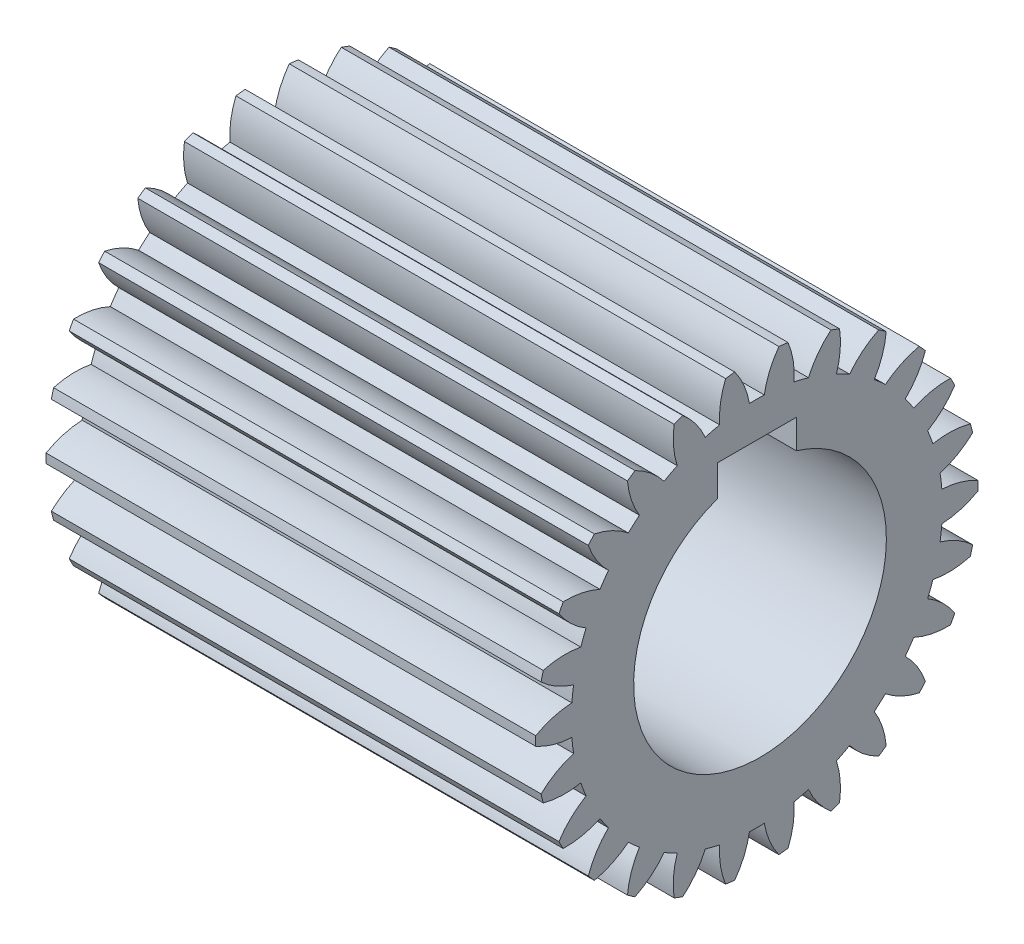
SolidWorks part; units mm, degrees
ref_plane "Plane1" through (0, 0, 0) normal (0, 0, 1) x (1, 0, 0)
ref_plane "Plane2" through (0, 0, 0) normal (0, 1, 0) x (1, 0, 0)
ref_plane "Plane3" through (0, 0, 0) normal (1, 0, 0) x (0, 0, -1)
sketch "HoldingSke" plane through (0, 0, 0) normal (0, 1, 0) x (1, 0, 0)
  line L0 (0, 0) -> (0.4494, -0.2192)
  line L1 (-15, 0) -> (100, 0) construction
  line L2 (0, 0) -> (-2.1039, 2.3779)
  line L3 (0, 0) -> (-11.863, 4.5341)
  line L4 (0, 0) -> (7.762, 3.7858)
  line L5 (0, 0) -> (-46.8476, -17.4728)
  line L6 (0, 0) -> (-51.3957, -34.6768)
  line L7 (-2.1039, 2.3779) -> (11.2416, 62.9246)
  line L8 (-76.2, 54.61) -> (-76.1, 54.61)
  line L9 (-71.009, 38.7566) -> (-53.1078, 45.2721)
  line L10 (-76.2, 71.12) -> (104.1128, 71.12)
  line L11 (0, 0) -> (-62, 0)
  line L12 (-76.2, 101.6) -> (-76.133, 101.6)
  line L13 (24.9733, 27.94) -> (52.9518, 28.4284)
  line L14 (24.9733, 27.94) -> (24.9743, 27.94)
  line L15 (24.9733, 27.94) -> (100.4006, 29.5858)
  line L16 (-63.627, -2) -> (-12.827, -2)
  circle A0 centre (0, 0) radius 0.4
  circle A1 centre (0, 0) radius 23.499
  circle A2 centre (0, 0) radius 37.5
  circle A3 centre (0, 0) radius 0.4
  dimension "MHD" = 46.998
  dimension "Hub_dia" = 75
  dimension "Bore" = 0.8
  dimension "MBD" = 0.8
  dimension "Num_teeth" = 26
  dimension "Pitch" = 0.5
  dimension "Overall_len" = 50
  dimension "Show_teeth" = 26
  dimension "Thickness" = 62
  dimension "OAL" = 62.0001
  dimension "T_dim" = 0.1
  dimension "Ap" = 20
  dimension "H" = 19.05
  dimension "Pitch_radius" = 180.3128
  dimension "Width" = 62
  dimension "Backlash" = 0.067
  dimension "Addendum_fac" = 1
  dimension "Dedendum_fac" = 1.25
  dimension "Clearance_fac" = 0.25
  dimension "Dedendum_add" = 0.001
  dimension "Module" = 2
sketch "BasProSke" plane through (0, 0, 0) normal (0, 1, 0) x (1, 0, 0)
  line L0 (-10, 0) -> (60, 0) construction
  line L1 (0, 0) -> (0, 28)
  line L2 (0, 0) -> (62, 0)
  line L3 (62, 0) -> (62, 28)
  line L4 (62, 28) -> (0, 28)
  dimension "Thickness" = 62
  dimension "Diameter" = 56
revolve "Base-Revolve" add sketch "BasProSke" angle 360 about L0
sketch "TooCutSke" plane through (0, 0, 0) normal (1, 0, 0) x (0, 0, -1)
  line L1 (0, 0) -> (0, 107) construction
  line L2 (0, 0) -> (-1.6871, 25.9452) construction
  line L3 (0, 0) -> (-6.2581, 51.5402) construction
  line L4 (-1.6871, 25.9452) -> (-3.1291, 25.7701) construction
  arc A0 (0.9399, 23.4802) -> (-0.9399, 23.4802) centre (0, 0) ccw
  arc A1 (2.8138, 27.8838) -> (-2.8138, 27.8838) centre (0, 0) ccw
  circle A2 centre (0, 0) radius 26 construction
  circle A3 centre (0, 0) radius 24.432 construction
  arc A4 (-0.9399, 23.4802) -> (-2.8138, 27.8838) centre (-11.1896, 21.719) ccw
  arc A5 (2.8138, 27.8838) -> (0.9399, 23.4802) centre (11.1896, 21.719) ccw
  dimension "Root_dia" = 46.998
  dimension "Overcut_dia" = 56.0508
  dimension "Pitch_dia" = 52
  dimension "Base_dia" = 48.864
  dimension "Flank_rad" = 10.4
  dimension "Half_ang" = 6.923
  dimension "Half_CT" = 1.4526
extrude "ToothCut" cut sketch "TooCutSke" along normal through all
fillet "Breaks" [suppressed] radius 0.04
fillet "RootFillets" [suppressed] radius 0.501
pattern_circular "TeethCuts" count 26 every 13.846 about axis through (-10, 0, 0) along (1, 0, 0) of "ToothCut", "RootFillets", "Breaks"
sketch "HubNeaOneSke" plane through (0, 0, 0) normal (-1, 0, 0) x (0, 0, 1)
  circle A0 centre (0, 0) radius 23.499
  dimension "Diameter" = 46.998
extrude "HubNearOne" [suppressed] add sketch "HubNeaOneSke" along normal blind 12.7001
sketch "HubNeaBotSke" plane through (0, 0, 0) normal (-1, 0, 0) x (0, 0, 1)
  circle A0 centre (0, 0) radius 23.499
  dimension "Diameter" = 46.998
extrude "HubNearBoth" [suppressed] add sketch "HubNeaBotSke" along normal blind 6.35
ref_plane "FarPln" through (62, 0, 0) normal (1, 0, 0) x (0, 0, -1)
sketch "HubFarSke" plane through (62, 0, 0) normal (1, 0, 0) x (0, 0, -1)
  circle A0 centre (0, 0) radius 23.499
  dimension "Diameter" = 46.998
extrude "HubFar" [suppressed] add sketch "HubFarSke" along normal blind 6.35
sketch "BorSke" plane through (0, 0, 0) normal (1, 0, 0) x (0, 0, -1)
  circle A0 centre (0, 0) radius 0.4
  dimension "Diameter" = 0.8
extrude "Bore" cut sketch "BorSke" along normal mid plane 124.0001
sketch "KeySke" plane through (0, 0, 0) normal (1, 0, 0) x (0, 0, -1)
  line L0 (-0.05, 0) -> (-0.05, 0.5)
  line L1 (-0.05, 0.5) -> (0.05, 0.5)
  line L2 (0.05, 0.5) -> (0.05, 0)
  line L3 (0, 0) -> (0, 34) construction
  line L4 (-0.05, 0) -> (0.05, 0)
  dimension "Offset" = 0.5
  dimension "Width" = 0.1
extrude "Keyway" [suppressed] cut sketch "KeySke" along normal mid plane 124.0001
pattern_circular "Keyway2" [suppressed] count 2 every 90 about axis through (-10, 0, 0) along (1, 0, 0)
sketch "Sketch1" plane through (62, 0, 0) normal (1, 0, 0) x (0, 0, -1)
  line L0 (0, 0) -> (0, 22.4761) construction
  line L2 (-5, 19) -> (5, 19)
  line L3 (-5, 19) -> (-5, 15.0612)
  line L5 (5, 19) -> (5, 15.3245)
  arc A0 (-5, 15.0612) -> (5, 15.3245) centre (0.4, 0) ccw
  circle A1 centre (0, 0) radius 0.4 construction
  dimension "D1" = 32
  dimension "D2" = 10
  dimension "D3" = 19
extrude "Cut-Extrude1" cut sketch "Sketch1" against normal through all contours A0 L5 L2 L3
equation "' \"Module@HoldingSke\" = 6.35"
equation "' \"Num_teeth@HoldingSke\" = 12"
equation "' \"Ap@HoldingSke\" =  20"
equation "' \"Ap@HoldingSke\" = 20"
equation "' \"Width@HoldingSke\" = 0.5 * 25.4"
equation "' \"Hub_dia@HoldingSke\"= 1 * 25.4"
equation "' \"Hub_dia@HoldingSke\" = 1 * 25.4"
equation "' \"Overall_len@HoldingSke\" = 1.0 * 25.4"
equation "' \"Bore@HoldingSke\" = 0.75 * 25.4"
equation "' \"T_dim@HoldingSke\" = 0.1 * 25.4"
equation "' \"Width@KeySke\" = 0.25 * 25.4"
equation "' \"Show_teeth@HoldingSke\" = 13"
equation "' \"Backlash@HoldingSke\" = 0.009 * 25.4"
equation "' \"Addendum_fac@HoldingSke\" = 1.0"
equation "' \"Dedendum_fac@HoldingSke\" = 1.25"
equation "' \"Dedendum_add@HoldingSke\" = 0.00005 * 25.4"
equation "' \"Clearance_fac@HoldingSke\" = 0.25"
equation "\"Pitch@HoldingSke\" = 1 / \"Module@HoldingSke\""
equation "\"Overcut_dia@TooCutSke\" = (\"Num_teeth@HoldingSke\" + 2 * \"Addendum_fac@HoldingSke\") / \"Pitch@HoldingSke\" + 0.002 * 25.4"
equation "\"Pitch_dia@TooCutSke\" = \"Num_teeth@HoldingSke\" / \"Pitch@HoldingSke\""
equation "\"Base_dia@TooCutSke\" = \"Num_teeth@HoldingSke\" / \"Pitch@HoldingSke\" * cos((\"Ap@HoldingSke\"  * 3.14159265 / 180))"
equation "\"Root_dia@TooCutSke\" = (\"Num_teeth@HoldingSke\" + 2) / \"Pitch@HoldingSke\" - 2 * (\"Addendum_fac@HoldingSke\" + \"Dedendum_fac@HoldingSke\") / \"Pitch@HoldingSke\" - \"Dedendum_add@HoldingSke\" * 2"
equation "\"Half_ang@TooCutSke\" = 180 / \"Num_teeth@HoldingSke\""
equation "\"Half_CT@TooCutSke\" = \"Num_teeth@HoldingSke\" / \"Pitch@HoldingSke\" * sin((3.14159265 / 2 / \"Num_teeth@HoldingSke\")) / 2 - 7 * \"Backlash@HoldingSke\" / 4"
equation "\"Flank_rad@TooCutSke\" = \"Num_teeth@HoldingSke\" / \"Pitch@HoldingSke\" / 5"
equation "\"Radius@RootFillets\" = \"Clearance_fac@HoldingSke\" / \"Pitch@HoldingSke\" + \"Dedendum_add@HoldingSke\""
equation "\"Break_rad@Breaks\" = 0.02 / \"Pitch@HoldingSke\""
equation "\"Thickness@HoldingSke\" = \"Width@HoldingSke\""
equation "\"OAL@HoldingSke\" = \"Thickness@HoldingSke\""
equation "\"MHD@HoldingSke\" = (\"Num_teeth@HoldingSke\" + 2) / \"Pitch@HoldingSke\" - 2 * (\"Addendum_fac@HoldingSke\" + \"Dedendum_fac@HoldingSke\")  / \"Pitch@HoldingSke\" - \"Dedendum_add@HoldingSke\" * 2"
equation "\"MBD@HoldingSke\" = (\"Num_teeth@HoldingSke\" + 2) / \"Pitch@HoldingSke\" - 2 * (\"Addendum_fac@HoldingSke\" + \"Dedendum_fac@HoldingSke\")  / \"Pitch@HoldingSke\" - \"Dedendum_add@HoldingSke\" * 2 - 0.002 * 25.4"
equation "\"MHD@HoldingSke\" = ((sgn( \"MHD@HoldingSke\" - \"Hub_dia@HoldingSke\" )-1)*( \"MHD@HoldingSke\" - \"Hub_dia@HoldingSke\" ))/-2+ \"Hub_dia@HoldingSke\""
equation "\"MBD@HoldingSke\" = ((sgn( \"MBD@HoldingSke\" - \"Bore@HoldingSke\" )-1)*( \"MBD@HoldingSke\" - \"Bore@HoldingSke\" ))/-2+ \"Bore@HoldingSke\""
equation "\"OAL@HoldingSke\" = ((sgn( \"OAL@HoldingSke\" - \"Overall_len@HoldingSke\" )+1)*( \"OAL@HoldingSke\" - \"Overall_len@HoldingSke\" ))/2 + \"Overall_len@HoldingSke\" + 0.000002 * 25.4"
equation "\"Num_teeth@TeethCuts\" = int( \"Show_teeth@HoldingSke\" ) + 1"
equation "\"Num_teeth@TeethCuts\" = ((sgn( \"Num_teeth@TeethCuts\" - \"Num_teeth@HoldingSke\" )-1)*( \"Num_teeth@TeethCuts\" - \"Num_teeth@HoldingSke\" ))/-2+ \"Num_teeth@HoldingSke\""
equation "\"Num_teeth@TeethCuts\" = ((sgn( \"Num_teeth@TeethCuts\" - 2.0)+1)*( \"Num_teeth@TeethCuts\" - 2.0))/2 +2.0"
equation "\"Angle@TeethCuts\" = 360.0 / \"Num_teeth@HoldingSke\""
equation "\"Diameter@BasProSke\" = (\"Num_teeth@HoldingSke\" + 2 * \"Addendum_fac@HoldingSke\") / \"Pitch@HoldingSke\""
equation "\"Thickness@BasProSke\"  = \"Thickness@HoldingSke\""
equation "' \"Fillet_rad@BasProSke\" =  \"Thickness@HoldingSke\" * 0.05"
equation "' \"Fillet_rad@BasProSke\" = \"Thickness@HoldingSke\" * 0.05"
equation "\"MHD@HoldingSke\" = ((sgn( \"MHD@HoldingSke\" - \"Root_dia@TooCutSke\" )-1)*( \"MHD@HoldingSke\" - \"Root_dia@TooCutSke\" ))/-2+ \"Root_dia@TooCutSke\""
equation "\"Diameter@HubNeaOneSke\" = \"MHD@HoldingSke\""
equation "\"Length@HubNearOne\" = \"OAL@HoldingSke\" - \"Thickness@BasProSke\""
equation "\"Diameter@HubNeaBotSke\" = \"MHD@HoldingSke\""
equation "\"Length@HubNearBoth\" = ( \"OAL@HoldingSke\" - \"Thickness@BasProSke\" ) / 2.0"
equation "\"Thickness@FarPln\" = \"Thickness@BasProSke\""
equation "\"Diameter@HubFarSke\" = \"MHD@HoldingSke\""
equation "\"Length@HubFar\" = ( \"OAL@HoldingSke\" - \"Thickness@BasProSke\" ) / 2.0"
equation "\"Diameter@BorSke\" = \"MBD@HoldingSke\""
equation "\"D1@Bore\" = \"OAL@HoldingSke\" * 2.0"
equation "\"D1@Keyway\" = \"OAL@HoldingSke\" * 2.0"
equation "\"Offset@KeySke\" = \"T_dim@HoldingSke\" + \"MBD@HoldingSke\" / 2.0"
